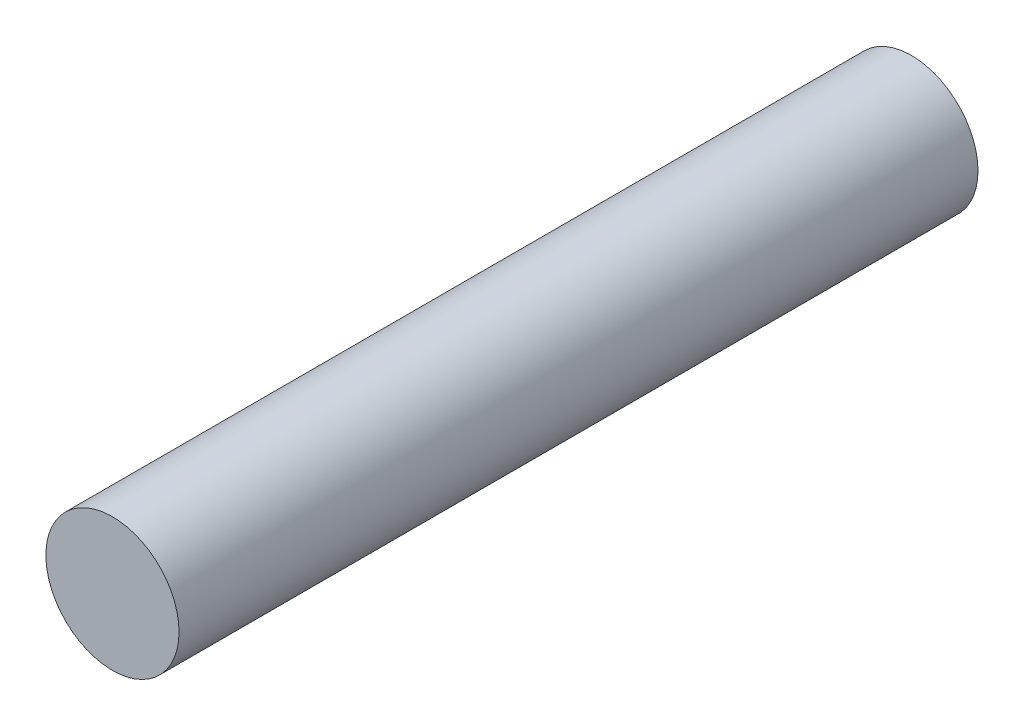
SolidWorks part; units mm, degrees
ref_plane "Front Plane" through (0, 0, 0) normal (0, 0, 1) x (1, 0, 0)
ref_plane "Top Plane" through (0, 0, 0) normal (0, 1, 0) x (1, 0, 0)
ref_plane "Right Plane" through (0, 0, 0) normal (1, 0, 0) x (0, 0, -1)
sketch "Sketch1" plane through (0, 0, 0) normal (0, 0, 1) x (1, 0, 0)
  circle A0 centre (0, 0) radius 6.35
  dimension "D1" = 12.7
extrude "Boss-Extrude1" add sketch "Sketch1" along normal blind 76.2
